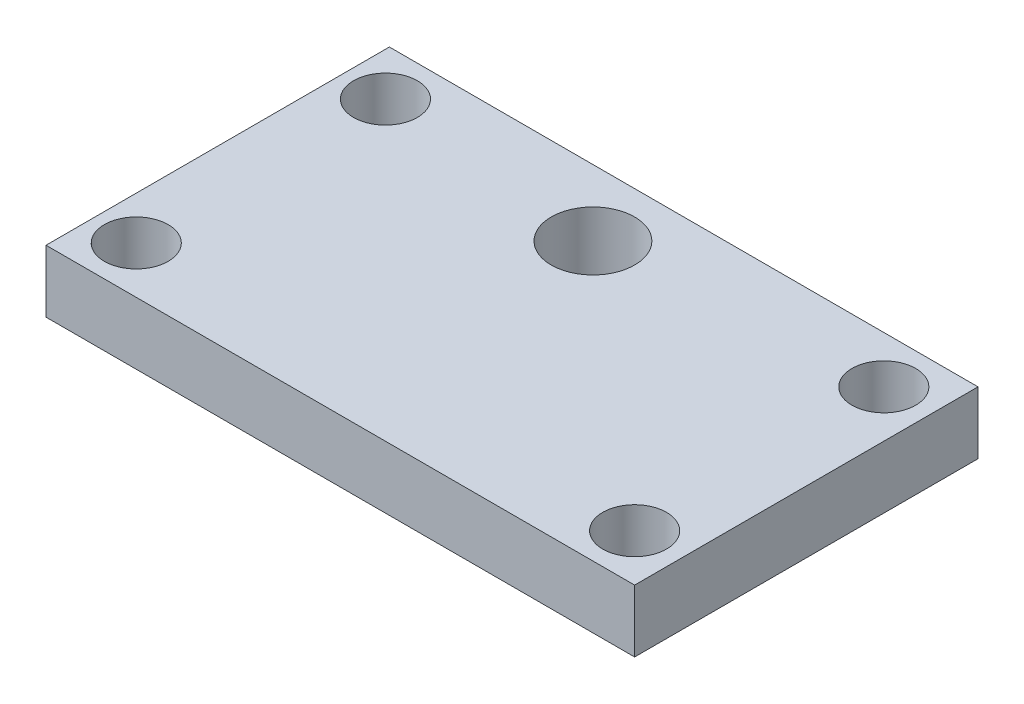
SolidWorks part; units mm, degrees
ref_plane "Front Plane" through (0, 0, 0) normal (0, 0, 1) x (1, 0, 0)
ref_plane "Top Plane" through (0, 0, 0) normal (0, 1, 0) x (1, 0, 0)
ref_plane "Right Plane" through (0, 0, 0) normal (1, 0, 0) x (0, 0, -1)
sketch "Sketch1" plane through (0, 0, 0) normal (0, 1, 0) x (1, 0, 0)
  line L1 (-30, -17.5) -> (30, -17.5)
  line L2 (-30, -17.5) -> (-30, 17.5)
  line L3 (-30, 17.5) -> (30, 17.5)
  line L4 (30, -17.5) -> (30, 17.5)
  line L5 (-30, -17.5) -> (30, 17.5) construction
  line L6 (-30, 17.5) -> (30, -17.5) construction
  circle A0 centre (-25.6, 12.7) radius 3.25
  circle A1 centre (25.2, 12.7) radius 3.25
  circle A2 centre (-25.6, -12.7) radius 3.25
  circle A3 centre (25.2, -12.7) radius 3.25
  point P0 (0, 0)
  point P12 (0, 0)
  point P15 (0, 0)
  point P16 (0, 0)
  point P17 (0, 0)
  point P18 (0, 0)
  point P19 (0, 0)
  point P20 (0, 0)
  point P21 (0, 0)
  dimension "D4" = 6.5
  dimension "D5" = 6.5
  dimension "D9" = 6.5
  dimension "D10" = 6.5
  dimension "D1" = 60
  dimension "D2" = 35
  dimension "D3" = 50.8
  dimension "D6" = 25.4
  dimension "D13" = 4.8
  dimension "D14" = 4.8
extrude "Boss-Extrude1" add sketch "Sketch1" along normal blind 6.35
sketch "Sketch2" plane through (0, 6.35, 0) normal (0, 1, 0) x (1, 0, 0)
  line L2 (-30, 17.5) -> (-30, -17.5) construction
  line L4 (30, 17.5) -> (-30, 17.5) construction
  circle A0 centre (-2.5, 10.75) radius 4.25
  point P8 (0, 0)
  dimension "D1" = 8.5
  dimension "D2" = 6.75
  dimension "D3" = 27.5
extrude "Cut-Extrude1" cut sketch "Sketch2" against normal through all
